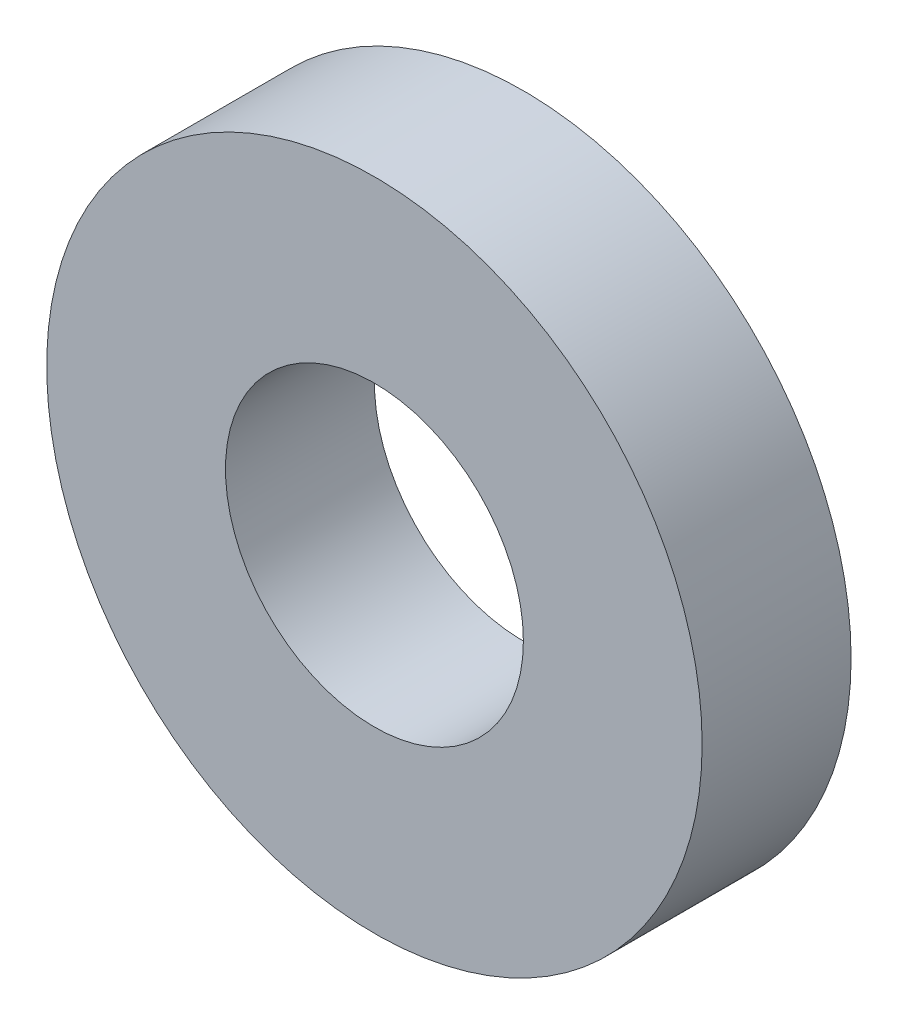
SolidWorks part; units mm, degrees
ref_plane "Front Plane" through (0, 0, 0) normal (0, 0, 1) x (1, 0, 0)
ref_plane "Top Plane" through (0, 0, 0) normal (0, 1, 0) x (1, 0, 0)
ref_plane "Right Plane" through (0, 0, 0) normal (1, 0, 0) x (0, 0, -1)
sketch "Sketch1" plane through (0, 0, 0) normal (0, 0, 1) x (1, 0, 0)
  circle A0 centre (0, 0) radius 6
  circle A1 centre (0, 0) radius 13.2
extrude "Boss-Extrude1" add sketch "Sketch1" along normal blind 6
sketch "Sketch2" plane through (0, 0, 6) normal (0, 0, 1) x (1, 0, 0)
  line L0 (0, 0) -> (0, 15.2) construction
  line L1 (-1.8199, 15.2) -> (0, 0) construction
  line L2 (1.8199, 15.2) -> (0, 0) construction
  arc A0 (-1.8199, 12) -> (1.8199, 12) centre (0, 0) cw
  arc A1 (-6.8199, 11.3018) -> (6.8199, 11.3018) centre (0, 0) cw
  arc A2 (-1.8199, 10.512) -> (1.8199, 10.512) centre (0, 0) cw
  arc A3 (-6.8199, 11.3018) -> (-1.8199, 12) centre (-4.3199, 11.6509) ccw
  arc A4 (6.8199, 11.3018) -> (1.8199, 10.512) centre (4.3199, 10.9069) ccw
  arc A5 (-1.8199, 12) -> (-6.8199, 11.3018) centre (-4.3199, 11.6509) cw
